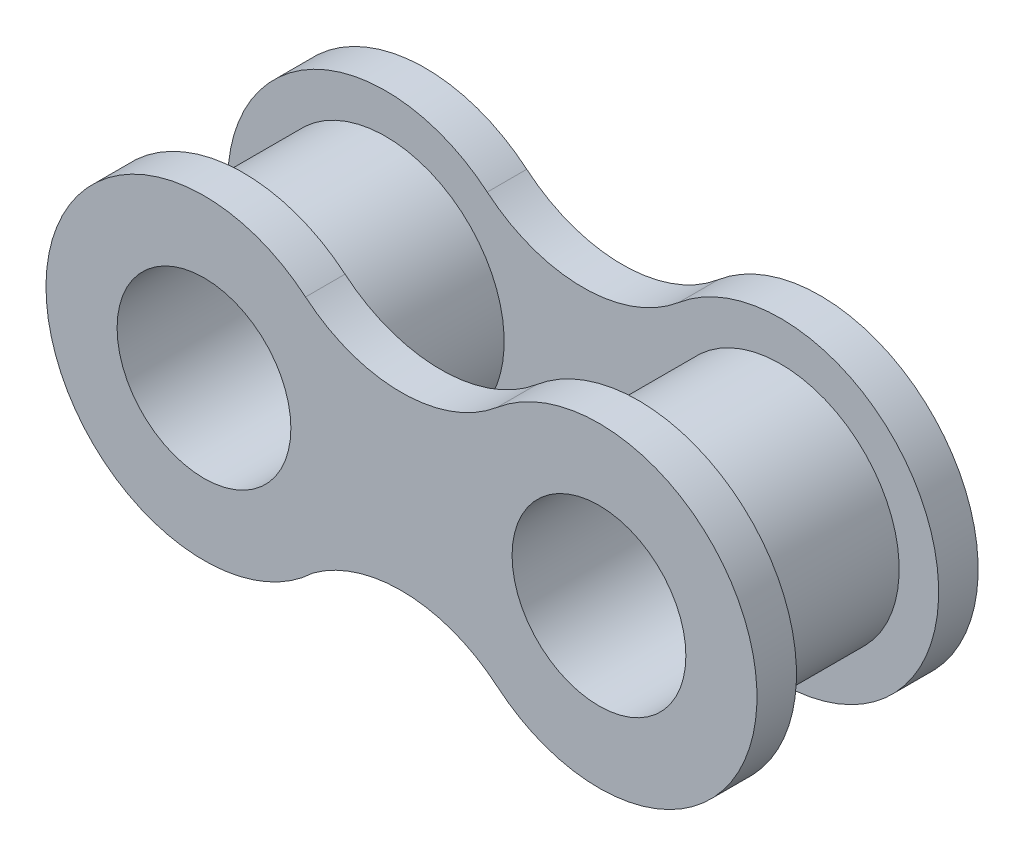
SolidWorks part; units mm, degrees
ref_plane "Front Plane" through (0, 0, 0) normal (0, 0, 1) x (1, 0, 0)
ref_plane "Top Plane" through (0, 0, 0) normal (0, 1, 0) x (1, 0, 0)
ref_plane "Right Plane" through (0, 0, 0) normal (1, 0, 0) x (0, 0, -1)
sketch "Sketch1" plane through (0, 0, 0) normal (0, 0, 1) x (1, 0, 0)
  line L0 (-25.6741, -9.9145) -> (-16.7579, -9.9145) construction
  arc A0 (-26.1918, -6.0371) -> (-25.9464, -13.599) centre (-29.4579, -9.9281) ccw
  arc A1 (-20.0323, -13.7984) -> (-20.0323, -6.0305) centre (-16.7579, -9.9145) ccw
  arc A2 (-26.1918, -6.0371) -> (-20.0323, -6.0305) centre (-23.116, -2.3728) ccw
  arc A3 (-25.9464, -13.599) -> (-20.0323, -13.7984) centre (-23.116, -17.4561) cw
  dimension "D1" = 10.16
  dimension "D2" = 10.16
  dimension "D3" = 12.7
extrude "Boss-Extrude1" add sketch "Sketch1" along normal blind 1.27
sketch "Sketch2" plane through (0, 0, 1.27) normal (0, 0, 1) x (1, 0, 0)
  circle A0 centre (-16.7579, -9.9145) radius 3.81
  circle A1 centre (-29.4579, -9.9281) radius 3.81
  dimension "D1" = 7.62
extrude "Boss-Extrude2" add sketch "Sketch2" along normal blind 4.572
ref_plane "Plane1" through (0, 0, 3.556) normal (0, 0, 1) x (1, 0, 0)
mirror "Mirror1" about plane through (0, 0, 3.556) normal (0, 0, 1) of "Boss-Extrude1"
sketch "Sketch5" plane through (0, 0, 7.112) normal (0, 0, 1) x (1, 0, 0)
  circle A0 centre (-29.4579, -9.9281) radius 2.794
  circle A1 centre (-16.7579, -9.9145) radius 2.794
  dimension "D1" = 5.588
extrude "Cut-Extrude1" cut sketch "Sketch5" against normal blind 24.638
sketch "Sketch6" plane through (0, 0, 0) normal (0, 0, 1) x (1, 0, 0)
  line L0 (-177.7743, 31.3581) -> (-176.7743, 31.3581) construction
  line L1 (-177.7743, 31.3581) -> (-177.7743, 32.3581) construction
  line L2 (-172.049, 94.5994) -> (212.3869, 59.7962)
  line L3 (240.8404, 22.9449) -> (230.6421, -38.1135)
  line L4 (226.4762, -45.5811) -> (173.7212, -91.7179)
  line L5 (163.1061, -94.6563) -> (-189.0467, -31.1334)
  arc A0 (-189.0467, -31.1334) -> (-172.049, 94.5994) centre (-177.7743, 31.3581) cw
  arc A1 (212.3869, 59.7962) -> (240.8404, 22.9449) centre (209.5243, 28.1755) cw
  arc A2 (230.6421, -38.1135) -> (226.4762, -45.5811) centre (218.1156, -36.0212) cw
  arc A3 (173.7212, -91.7179) -> (163.1061, -94.6563) centre (165.3606, -82.1581) cw
